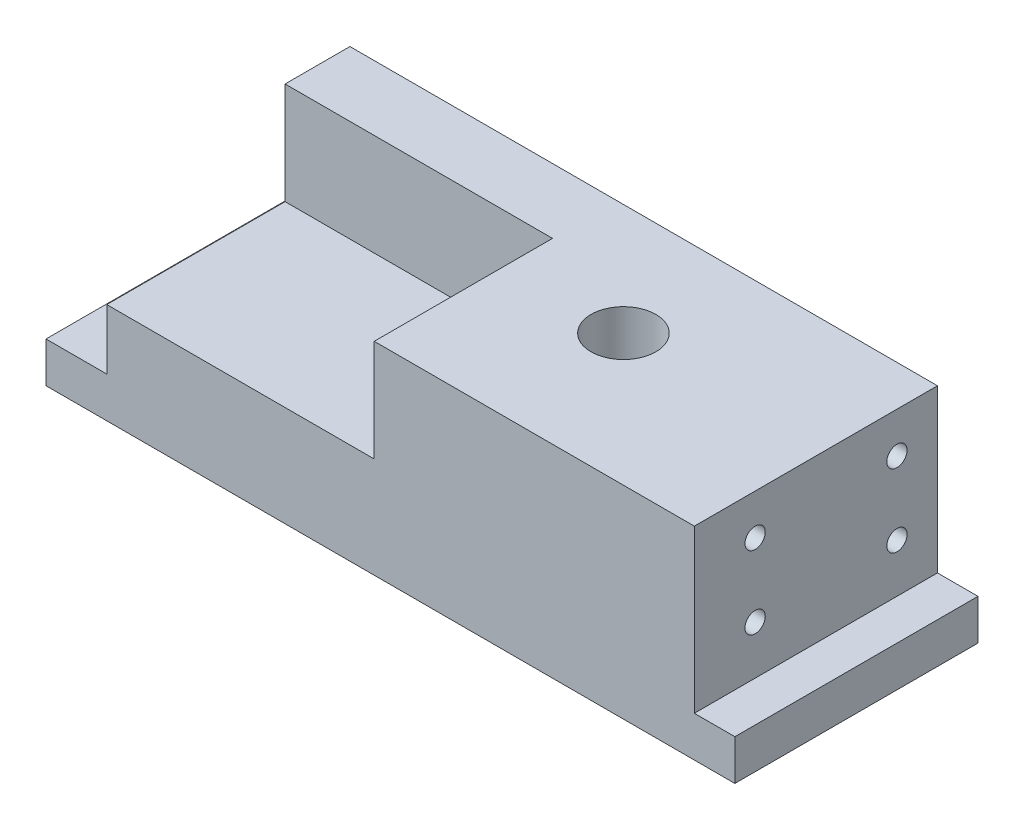
SolidWorks part; units mm, degrees
ref_plane "Ebene vorne" through (0, 0, 0) normal (0, 0, 1) x (1, 0, 0)
ref_plane "Ebene oben" through (0, 0, 0) normal (0, 1, 0) x (1, 0, 0)
ref_plane "Ebene rechts" through (0, 0, 0) normal (1, 0, 0) x (0, 0, -1)
sketch "Skizze1" plane through (0, 0, 0) normal (0, 0, 1) x (1, 0, 0)
  line L0 (0, 0) -> (168, 0)
  line L1 (168, 0) -> (168, 10)
  line L2 (168, 10) -> (158, 10)
  line L3 (158, 10) -> (158, 50)
  line L4 (158, 50) -> (13, 50)
  line L5 (13, 50) -> (13, 10)
  line L6 (13, 10) -> (0, 10)
  line L7 (0, 10) -> (0, 0)
  dimension "D1" = 13
  dimension "D2" = 10
  dimension "D3" = 145
  dimension "D4" = 40
  dimension "D5" = 40
  dimension "D6" = 10
extrude "Aufsatz-Linear austragen1" add sketch "Skizze1" along normal blind 65
sketch "Skizze3" plane through (0, 0, 0) normal (0, -1, 0) x (-1, 0, 0)
  line L0 (0, 0) -> (-168, 0) construction
  line L1 (-168, -65) -> (-168, 0) construction
  circle A0 centre (-108, -32.5) radius 8
  point P4 (-168, -32.5)
  dimension "D1" = 16
  dimension "D2" = 32.5
  dimension "D3" = 60
extrude "Schnitt-Linear austragen2" cut sketch "Skizze3" against normal blind 85
sketch "Skizze4" plane through (0, 0, 0) normal (0, 0, -1) x (-1, 0, 0)
  line L1 (-13, 50) -> (-79, 50)
  line L2 (-13, 50) -> (-13, 24.85)
  line L3 (-13, 24.85) -> (-79, 24.85)
  line L4 (-79, 50) -> (-79, 24.85)
  dimension "D1" = 25.15
  dimension "D2" = 66
extrude "Schnitt-Linear austragen3" cut sketch "Skizze4" against normal blind 120
sketch "Skizze5" plane through (158, 0, 0) normal (1, 0, 0) x (0, 0, -1)
  line L0 (-65, 10) -> (0, 10) construction
  line L1 (-65, 10) -> (-65, 50) construction
  line L2 (0, 10) -> (0, 50) construction
  circle A0 centre (-50, 40) radius 2.5
  circle A1 centre (-50, 22) radius 2.5
  circle A3 centre (-15, 22) radius 2.5
  circle A4 centre (-15, 40) radius 2.5
  dimension "D1" = 5
  dimension "D2" = 5
  dimension "D3" = 5
  dimension "D4" = 5
  dimension "D5" = 12
  dimension "D6" = 15
  dimension "D7" = 15
  dimension "D8" = 12
  dimension "D9" = 30
  dimension "D10" = 30
  dimension "D11" = 15
  dimension "D12" = 15
extrude "Schnitt-Linear austragen4" cut sketch "Skizze5" against normal blind 15
cosmetic thread "Gewindedarstellung1" parameters "D1"=15, "D2"=6
cosmetic thread "Gewindedarstellung2" parameters "D1"=15, "D2"=6
cosmetic thread "Gewindedarstellung3" parameters "D1"=15, "D2"=6
cosmetic thread "Gewindedarstellung4" parameters "D1"=15, "D2"=6
sketch "Skizze6" plane through (13, 0, 0) normal (-1, 0, 0) x (0, 0, 1)
  line L0 (0, 24.85) -> (0, 10) construction
  line L1 (65, 24.85) -> (65, 10) construction
  line L2 (65, 10) -> (0, 10) construction
  circle A0 centre (15, 18) radius 2.5
  circle A1 centre (50, 18) radius 2.5
  dimension "D1" = 5
  dimension "D2" = 5
  dimension "D3" = 15
  dimension "D4" = 15
  dimension "D5" = 8
  dimension "D6" = 8
extrude "Schnitt-Linear austragen5" cut sketch "Skizze6" against normal blind 12
cosmetic thread "Gewindedarstellung5" parameters "D1"=12, "D2"=6
cosmetic thread "Gewindedarstellung6" parameters "D1"=12, "D2"=6
sketch "Skizze7" plane through (13, 0, 0) normal (-1, 0, 0) x (0, 0, 1)
  line L0 (65, 24.85) -> (65, 10) construction
  line L1 (0, 24.85) -> (21, 24.85)
  line L2 (0, 24.85) -> (0, 50)
  line L3 (0, 50) -> (21, 50)
  line L4 (21, 24.85) -> (21, 50)
  dimension "D1" = 44
  dimension "D2" = 25.15
extrude "Aufsatz-Linear austragen2" add sketch "Skizze7" against normal blind 66
sketch "Skizze8" plane through (13, 0, 0) normal (-1, 0, 0) x (0, 0, 1)
  line L0 (0, 50) -> (0, 10) construction
  line L1 (65, 10) -> (0, 10) construction
  circle A0 centre (15, 40) radius 2.5
  dimension "D1" = 5
  dimension "D2" = 15
  dimension "D3" = 30
extrude "Schnitt-Linear austragen7" cut sketch "Skizze8" against normal blind 12
cosmetic thread "Gewindedarstellung7" parameters "D1"=12, "D2"=6
sketch "Skizze9" plane through (0, 0, 0) normal (0, 0, -1) x (-1, 0, 0)
  line L0 (0, 0) -> (0, 10)
  line L1 (0, 10) -> (-13, 10)
  line L2 (-13, 10) -> (-13, 50)
  line L3 (-13, 50) -> (-158, 50)
  line L4 (-158, 50) -> (-158, 10)
  line L5 (-158, 10) -> (-168, 10)
  line L6 (-168, 10) -> (-168, 0)
  line L7 (-168, 0) -> (0, 0)
extrude "Schnitt-Linear austragen8" cut sketch "Skizze9" against normal blind 5
sketch "Skizze10" plane through (0, 0, 0) normal (-1, 0, 0) x (0, 0, 1)
  line L1 (5, 10) -> (65, 10)
  line L2 (5, 10) -> (5, 0)
  line L3 (5, 0) -> (65, 0)
  line L4 (65, 10) -> (65, 0)
extrude "Aufsatz-Linear austragen3" add sketch "Skizze10" along normal blind 2
